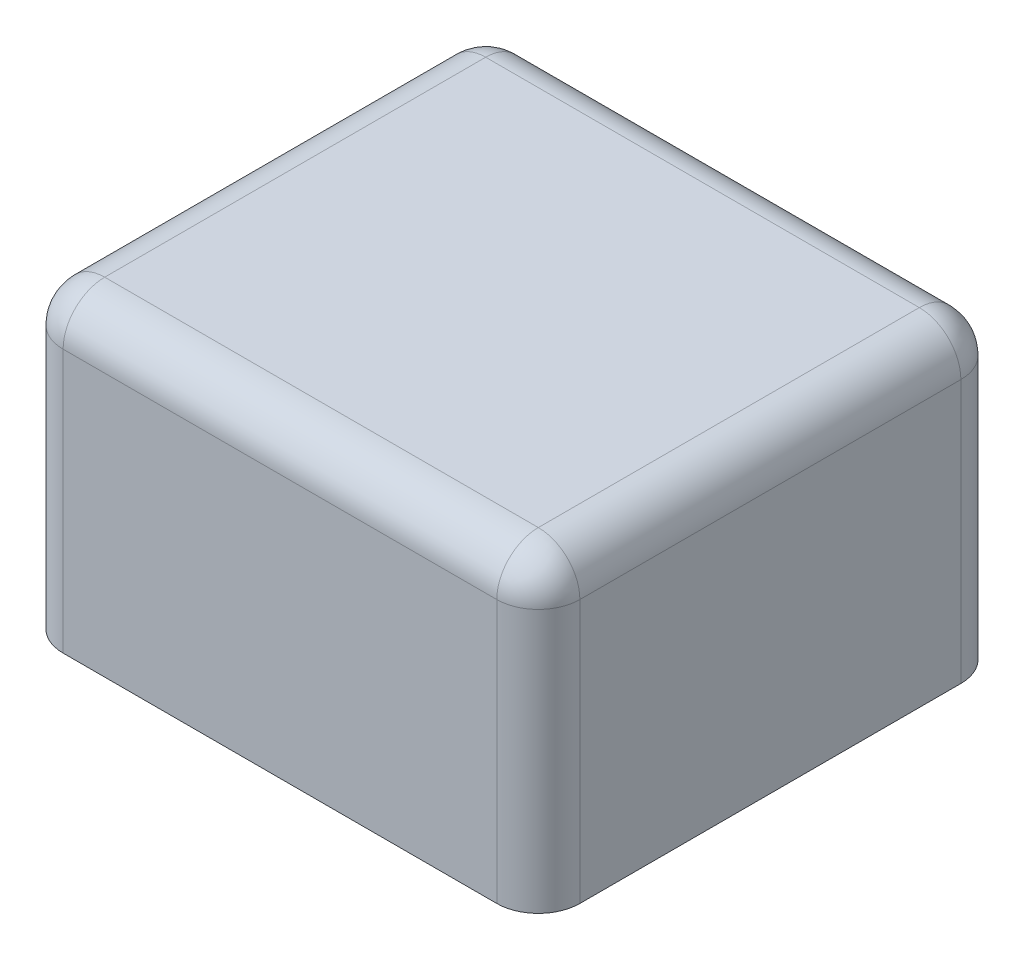
SolidWorks part; units mm, degrees
ref_plane "Alzado" through (0, 0, 0) normal (0, 0, 1) x (1, 0, 0)
ref_plane "Planta" through (0, 0, 0) normal (0, 1, 0) x (1, 0, 0)
ref_plane "Vista lateral" through (0, 0, 0) normal (1, 0, 0) x (0, 0, -1)
sketch "Croquis1" plane through (0, 0, 0) normal (0, 1, 0) x (1, 0, 0)
  line L1 (-18.65, -16.75) -> (18.65, -16.75)
  line L2 (-18.65, -16.75) -> (-18.65, 16.75)
  line L3 (-18.65, 16.75) -> (18.65, 16.75)
  line L4 (18.65, -16.75) -> (18.65, 16.75)
  line L5 (-18.65, -16.75) -> (18.65, 16.75) construction
  line L6 (-18.65, 16.75) -> (18.65, -16.75) construction
  point P0 (0, 0)
  dimension "D1" = 37.3
  dimension "D2" = 33.5
extrude "Saliente-Extruir1" add sketch "Croquis1" along normal blind 22
fillet "Redondeo1" radius 3 8 edges at (-18.65, 11, -16.75) (18.65, 11, -16.75) (18.65, 11, 16.75) (-18.65, 11, 16.75) (0, 22, -16.75) (18.65, 22, 0) (0, 22, 16.75) (-18.65, 22, 0)
